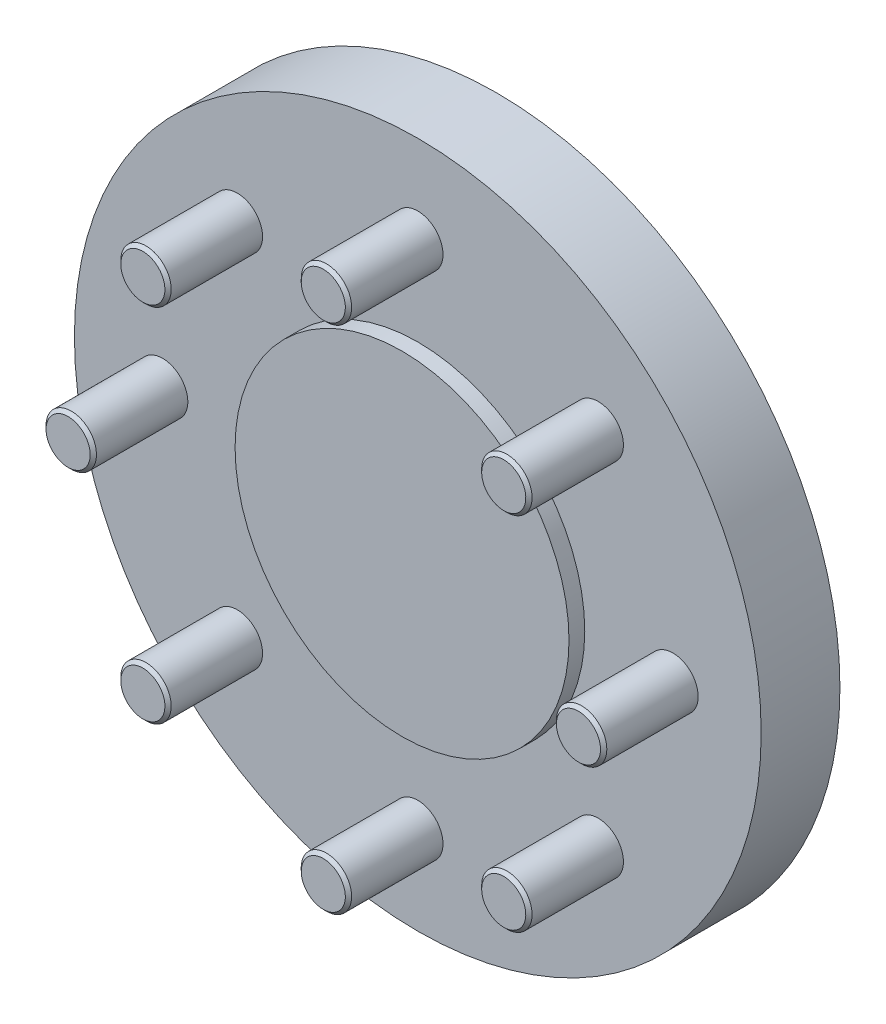
SolidWorks part; units mm, degrees
ref_plane "Front Plane" through (0, 0, 0) normal (0, 0, 1) x (1, 0, 0)
ref_plane "Top Plane" through (0, 0, 0) normal (0, 1, 0) x (1, 0, 0)
ref_plane "Right Plane" through (0, 0, 0) normal (1, 0, 0) x (0, 0, -1)
sketch "Sketch1" plane through (0, 0, 0) normal (0, 1, 0) x (1, 0, 0)
  line L0 (0, 0) -> (0, 75)
  line L1 (0, 75) -> (30, 75)
  line L2 (30, 75) -> (30, 30)
  line L3 (30, 30) -> (109, 30)
  line L4 (109, 30) -> (109, 5)
  line L5 (109, 5) -> (53, 5)
  line L6 (53, 5) -> (53, 0)
  line L7 (53, 0) -> (0, 0)
  dimension "D1" = 75
  dimension "D2" = 53
  dimension "D3" = 56
  dimension "D4" = 25
  dimension "D5" = 45
  dimension "D6" = 30
revolve "Revolve1" add sketch "Sketch1" angle 360 about L0
sketch "Sketch2" plane through (0, 0, -5) normal (0, 0, 1) x (1, 0, 0)
  circle A0 centre (81, 0) radius 8
  point P2 (0, 0)
  dimension "D1" = 16
  dimension "D2" = 81
extrude "Boss-Extrude1" add sketch "Sketch2" along normal blind 30
chamfer "Chamfer1" distance 1 angle 45 1 edges at (89, 0, 25)
pattern_circular "CirPattern1" count 8 over 360 about axis through (0, 0, 0) along (0, 0, 1) of "Chamfer1", "Boss-Extrude1"
